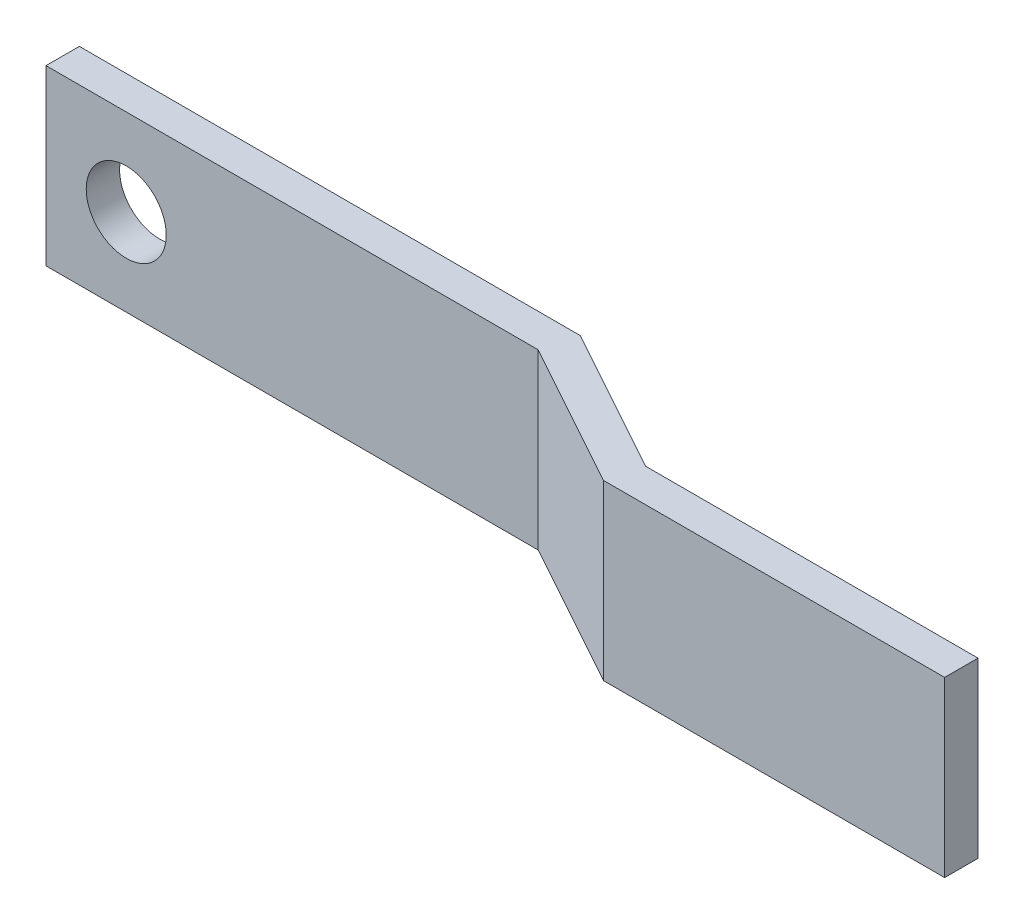
SolidWorks part; units mm, degrees
ref_plane "Front Plane" through (0, 0, 0) normal (0, 0, 1) x (1, 0, 0)
ref_plane "Top Plane" through (0, 0, 0) normal (0, 1, 0) x (1, 0, 0)
ref_plane "Right Plane" through (0, 0, 0) normal (1, 0, 0) x (0, 0, -1)
sketch "Sketch1" plane through (0, 0, 0) normal (0, 1, 0) x (1, 0, 0)
  line L0 (0, 0) -> (38.1391, 0)
  line L1 (38.1391, 0) -> (49.2453, -6.1289)
  line L2 (49.2453, -6.1289) -> (74.5674, -6.1289)
extrude "Extrude-Thin1" add sketch "Sketch1" along normal blind 13.208 thin
sketch "Sketch3" plane through (0, 0, 0) normal (0, 0, -1) x (-1, 0, 0)
  circle A0 centre (-6.1106, 6.604) radius 3.048
extrude "Cut-Extrude1" cut sketch "Sketch3" against normal up to next
